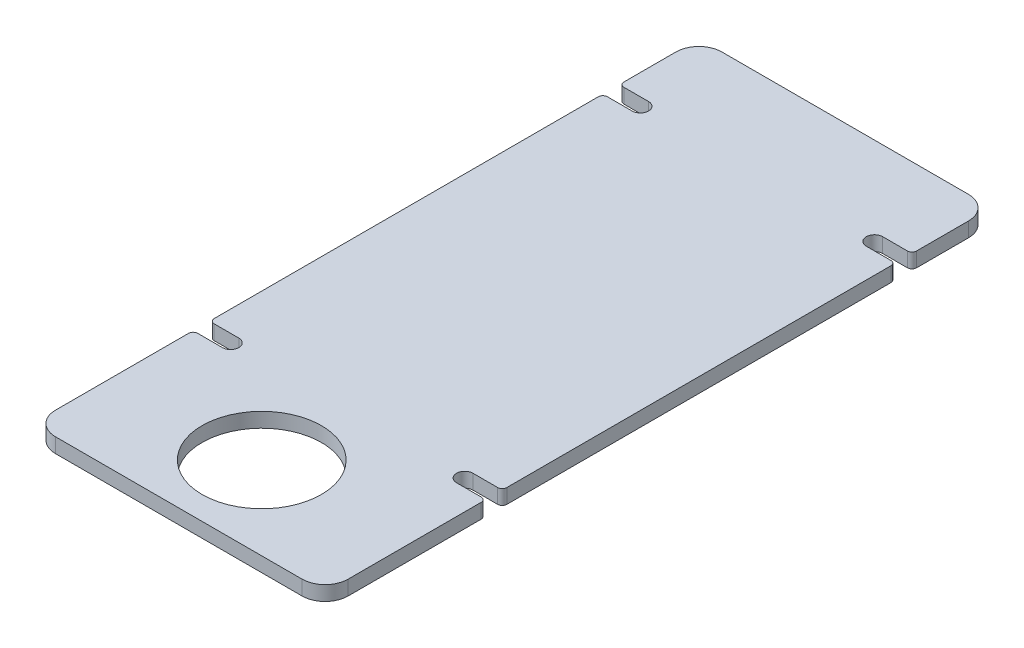
SolidWorks part; units mm, degrees
material "6061-T6 (SS)"
ref_plane "Front Plane" through (0, 0, 0) normal (0, 0, 1) x (1, 0, 0)
ref_plane "Top Plane" through (0, 0, 0) normal (0, 1, 0) x (1, 0, 0)
ref_plane "Right Plane" through (0, 0, 0) normal (1, 0, 0) x (0, 0, -1)
sketch "Sketch1" plane through (0, 0, 0) normal (0, 1, 0) x (1, 0, 0)
  line L0 (0, 0) -> (0, 15.8898) construction
  line L1 (0, 0) -> (19.991, 0) construction
  line L2 (-63.5, 215.1) -> (-31.3697, 215.1) construction
  line L3 (-63.5, -36) -> (63.5, -36)
  line L4 (-63.5, -36) -> (-63.5, 253.2)
  line L5 (-63.5, 253.2) -> (63.5, 253.2)
  line L6 (63.5, -36) -> (63.5, 253.2)
  line L7 (-63.5, 37.3) -> (-38.1, 37.3) construction
  line L8 (-76.2, 215.1) -> (-50.8, 215.1) construction
  line L9 (-76.2, 218.6719) -> (-50.8, 218.6719) construction
  line L10 (-76.2, 211.5281) -> (-50.8, 211.5281) construction
  line L11 (-76.2, 37.3) -> (-50.8, 37.3) construction
  line L12 (-76.2, 40.8719) -> (-50.8, 40.8719) construction
  line L13 (-76.2, 33.7281) -> (-50.8, 33.7281) construction
  circle A0 centre (0, 0) radius 25.9
  arc A1 (-76.2, 218.6719) -> (-76.2, 211.5281) centre (-76.2, 215.1) ccw construction
  arc A2 (-50.8, 211.5281) -> (-50.8, 218.6719) centre (-50.8, 215.1) ccw construction
  arc A3 (-76.2, 40.8719) -> (-76.2, 33.7281) centre (-76.2, 37.3) ccw construction
  arc A4 (-50.8, 33.7281) -> (-50.8, 40.8719) centre (-50.8, 37.3) ccw construction
  point P9 (0, -36)
  point P16 (-63.5, 215.1)
  point P22 (-63.5, 37.3)
  dimension "D1" = 51.8
  dimension "D2" = 127
  dimension "D3" = 36
  dimension "D4" = 253.2
  dimension "D5" = 215.1
  dimension "D6" = 37.3
  dimension "D7" = 7.1437
  dimension "D8" = 7.1437
  dimension "D9" = 12.7
  dimension "D10" = 12.7
extrude "Boss-Extrude1" add sketch "Sketch1" along normal blind 6.35
sketch "Sketch3" plane through (0, 6.35, 0) normal (0, 1, 0) x (1, 0, 0)
  line L0 (-76.2, 218.6719) -> (-50.8, 218.6719) construction
  line L1 (-76.2, 211.5281) -> (-50.8, 211.5281) construction
  line L2 (-76.2, 40.8719) -> (-50.8, 40.8719) construction
  line L3 (-76.2, 33.7281) -> (-50.8, 33.7281) construction
  line L4 (-76.2, 218.6719) -> (-50.8, 218.6719)
  line L5 (-76.2, 211.5281) -> (-50.8, 211.5281)
  line L6 (-76.2, 40.8719) -> (-50.8, 40.8719)
  line L7 (-76.2, 33.7281) -> (-50.8, 33.7281)
  arc A0 (-50.8, 211.5281) -> (-50.8, 218.6719) centre (-50.8, 215.1) ccw construction
  arc A1 (-76.2, 218.6719) -> (-76.2, 211.5281) centre (-76.2, 215.1) ccw construction
  arc A2 (-50.8, 33.7281) -> (-50.8, 40.8719) centre (-50.8, 37.3) ccw construction
  arc A3 (-76.2, 40.8719) -> (-76.2, 33.7281) centre (-76.2, 37.3) ccw construction
  arc A4 (-50.8, 211.5281) -> (-50.8, 218.6719) centre (-50.8, 215.1) ccw
  arc A5 (-76.2, 218.6719) -> (-76.2, 211.5281) centre (-76.2, 215.1) ccw
  arc A6 (-50.8, 33.7281) -> (-50.8, 40.8719) centre (-50.8, 37.3) ccw
  arc A7 (-76.2, 40.8719) -> (-76.2, 33.7281) centre (-76.2, 37.3) ccw
extrude "Cut-Extrude1" cut sketch "Sketch3" against normal through all
mirror "Mirror1" about plane through (0, 0, 0) normal (1, 0, 0) of "Cut-Extrude1"
fillet "Fillet1" radius 2 8 edges at (-63.5, 3.175, -40.8719) (-63.5, 3.175, -33.7281) (63.5, 3.175, -33.7281) (63.5, 3.175, -40.8719) (63.5, 3.175, -211.5281) (63.5, 3.175, -218.6719) (-63.5, 3.175, -211.5281) (-63.5, 3.175, -218.6719)
fillet "Fillet2" radius 10 4 edges at (-63.5, 3.175, 36) (63.5, 3.175, 36) (63.5, 3.175, -253.2) (-63.5, 3.175, -253.2)
